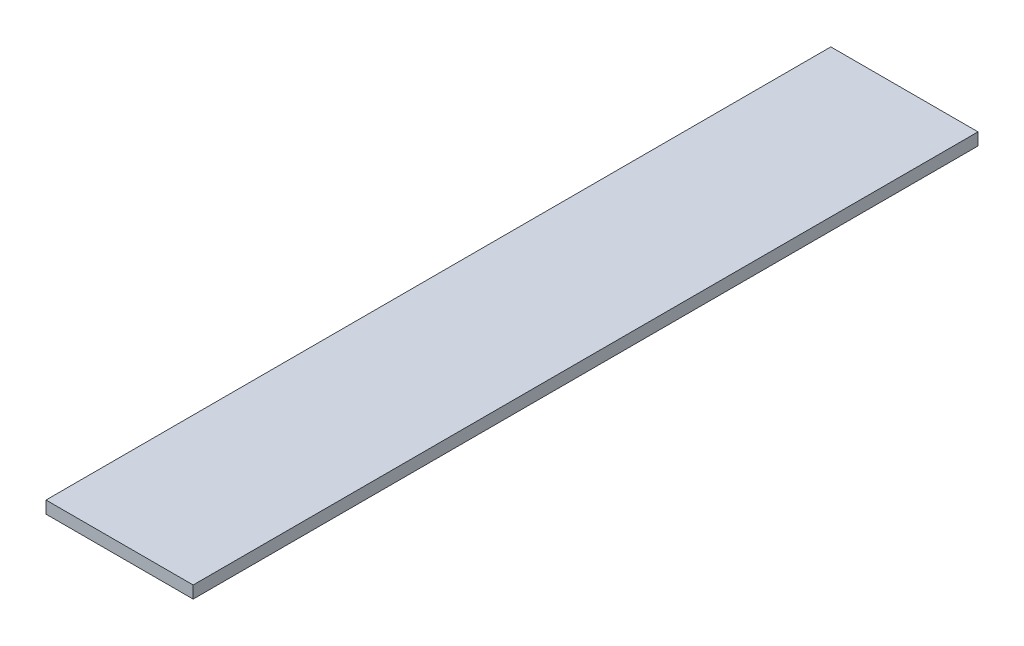
SolidWorks part; units mm, degrees
material "Delrin 2700 NC010, Low Viscosity Acetal Copolymer (SS)"
ref_plane "Front Plane" through (0, 0, 0) normal (0, 0, 1) x (1, 0, 0)
ref_plane "Top Plane" through (0, 0, 0) normal (0, 1, 0) x (1, 0, 0)
ref_plane "Right Plane" through (0, 0, 0) normal (1, 0, 0) x (0, 0, -1)
sketch "Sketch1" plane through (0, 0, 0) normal (0, 0, 1) x (1, 0, 0)
  line L1 (-9.525, -0.7938) -> (9.525, -0.7938)
  line L2 (-9.525, -0.7938) -> (-9.525, 0.7937)
  line L3 (-9.525, 0.7937) -> (9.525, 0.7937)
  line L4 (9.525, -0.7938) -> (9.525, 0.7937)
  line L5 (-9.525, -0.7938) -> (9.525, 0.7937) construction
  line L6 (-9.525, 0.7937) -> (9.525, -0.7938) construction
  point P0 (0, 0)
  dimension "D1" = 1.5875
  dimension "D2" = 19.05
extrude "Boss-Extrude1" add sketch "Sketch1" along normal blind 101.6
